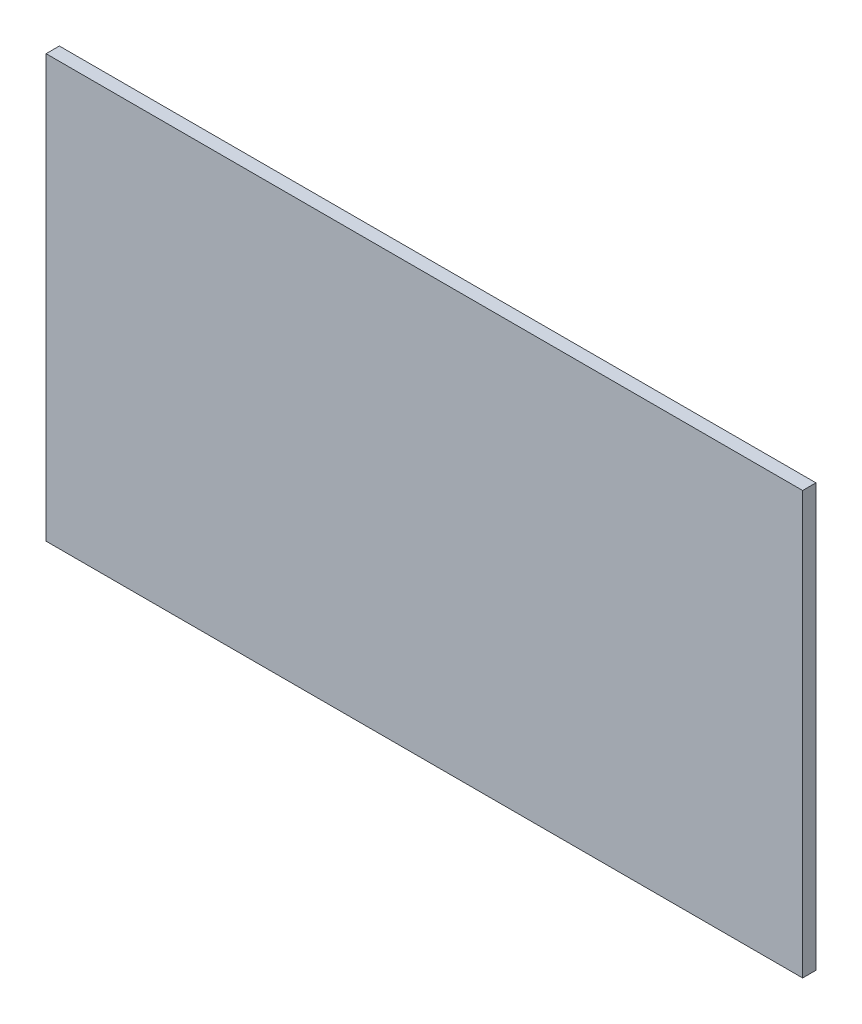
SolidWorks part; units mm, degrees
ref_plane "Front Plane" through (0, 0, 0) normal (0, 0, 1) x (1, 0, 0)
ref_plane "Top Plane" through (0, 0, 0) normal (0, 1, 0) x (1, 0, 0)
ref_plane "Right Plane" through (0, 0, 0) normal (1, 0, 0) x (0, 0, -1)
sketch "Sketch1" plane through (0, 0, 0) normal (0, 0, 1) x (1, 0, 0)
  line L1 (512.5, -286) -> (-512.5, -286)
  line L2 (512.5, -286) -> (512.5, 286)
  line L3 (512.5, 286) -> (-512.5, 286)
  line L4 (-512.5, -286) -> (-512.5, 286)
  line L5 (512.5, -286) -> (-512.5, 286) construction
  line L6 (512.5, 286) -> (-512.5, -286) construction
  point P0 (0, 0)
  dimension "D1" = 572
  dimension "D2" = 1025
extrude "Boss-Extrude1" add sketch "Sketch1" along normal blind 18
sketch "Sketch2" plane through (0, 0, 0) normal (0, 0, -1) x (-1, 0, 0)
  line L0 (512.5, 286) -> (512.5, -286) construction
  line L1 (112.5, -186) -> (312.5, -186)
  line L2 (112.5, -186) -> (112.5, 14)
  line L3 (112.5, 14) -> (312.5, 14)
  line L4 (312.5, -186) -> (312.5, 14)
  line L5 (112.5, -186) -> (312.5, 14) construction
  line L6 (112.5, 14) -> (312.5, -186) construction
  line L7 (512.5, -286) -> (-512.5, -286) construction
  point P0 (212.5, -86)
  dimension "D1" = 200
  dimension "D2" = 100
  dimension "D3" = 200
  dimension "D4" = 200
extrude "Cut-Extrude1" [suppressed] cut sketch "Sketch2" against normal through all
equation "\"H_DSP\"=18"
equation "\"D1@Boss-Extrude1\"=\"H_DSP\""
